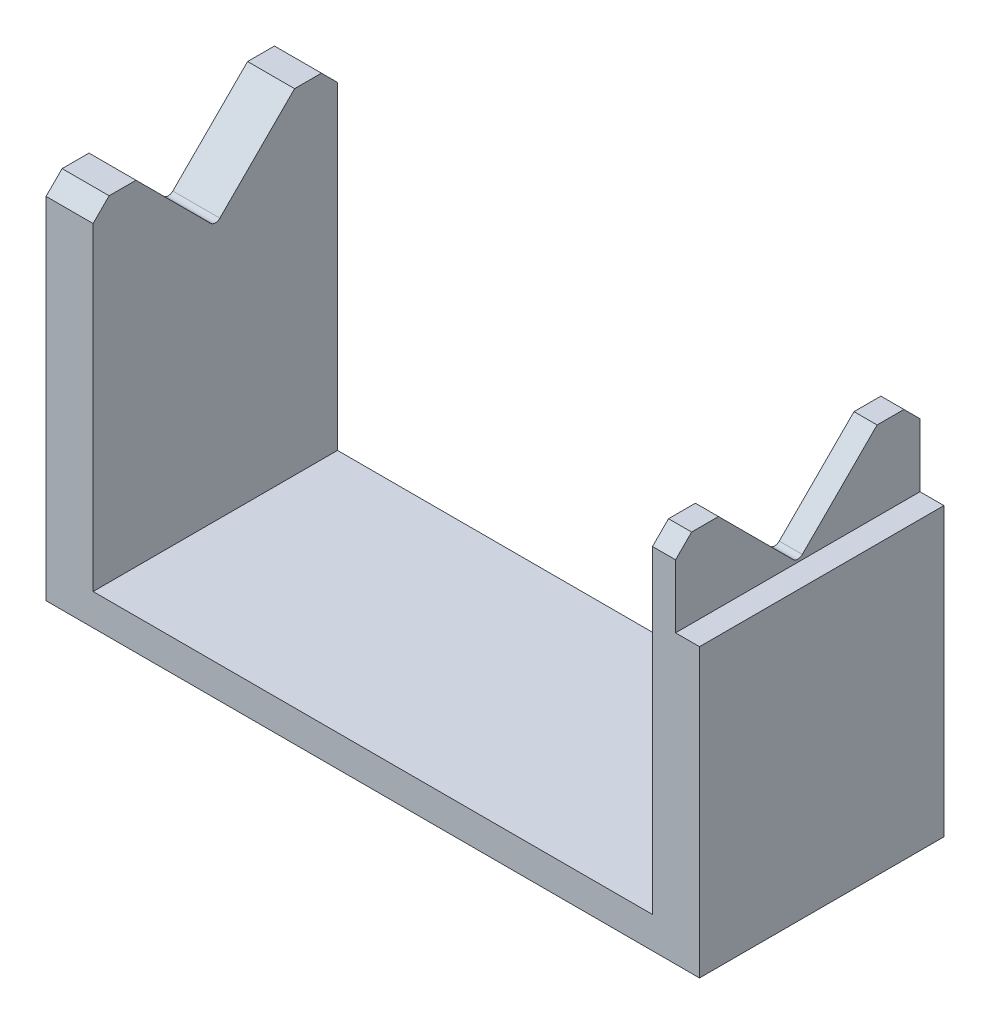
SolidWorks part; units mm, degrees
ref_plane "Plano frontal" through (0, 0, 0) normal (0, 0, 1) x (1, 0, 0)
ref_plane "Plano superior" through (0, 0, 0) normal (0, 1, 0) x (1, 0, 0)
ref_plane "Plano direito" through (0, 0, 0) normal (1, 0, 0) x (0, 0, -1)
sketch "Esboço1" plane through (0, 0, 0) normal (0, 1, 0) x (1, 0, 0)
  line L1 (50.93, -19.05) -> (-50.93, -19.05)
  line L2 (50.93, -19.05) -> (50.93, 19.05)
  line L3 (50.93, 19.05) -> (-50.93, 19.05)
  line L4 (-50.93, -19.05) -> (-50.93, 19.05)
  line L5 (50.93, -19.05) -> (-50.93, 19.05) construction
  line L6 (50.93, 19.05) -> (-50.93, -19.05) construction
  point P0 (0, 0)
  dimension "D1" = 101.86
  dimension "D2" = 38.1
extrude "Ressalto-extrusão1" add sketch "Esboço1" along normal blind 57.09
sketch "Esboço2" plane through (0, 0, 19.05) normal (0, 0, 1) x (1, 0, 0)
  line L0 (-43.6, 57.09) -> (43.6, 57.09)
  line L5 (-43.6, 57.09) -> (-43.6, 0)
  line L6 (-43.6, 57.09) -> (-43.6, 4.91)
  line L8 (43.6, 57.09) -> (43.6, 0)
  line L9 (43.6, 57.09) -> (43.6, 4.91)
  line L11 (-50.93, 4.91) -> (50.93, 4.91)
  line L12 (-43.6, 4.91) -> (43.6, 4.91)
  dimension "D1" = 7.33
  dimension "D2" = 7.33
  dimension "D3" = 4.91
extrude "Corte-extrusão1" cut sketch "Esboço2" against normal blind 57.09
sketch "Esboço4" plane through (0, 0, 19.05) normal (0, 0, 1) x (1, 0, 0)
  line L1 (50.93, 57.09) -> (50.93, 0) construction
  line L2 (50.93, 44.73) -> (47.2, 44.73) construction
  line L4 (47.2, 44.73) -> (50.93, 44.73)
  line L5 (47.2, 44.73) -> (47.2, 57.09)
  line L6 (47.2, 57.09) -> (50.93, 57.09)
  line L7 (50.93, 44.73) -> (50.93, 57.09)
extrude "Corte-extrusão2" cut sketch "Esboço4" against normal blind 57.09
sketch "Esboço5" plane through (47.2, 0, 0) normal (1, 0, 0) x (0, 0, -1)
  line L0 (0, 44.73) -> (0, 57.09) construction
  line L1 (19.05, 44.73) -> (-19.05, 44.73) construction
  line L2 (19.05, 57.09) -> (-19.05, 57.09) construction
  line L3 (0, 44.73) -> (-12.36, 57.09)
  line L4 (0, 44.73) -> (12.36, 57.09)
  line L5 (-12.36, 57.09) -> (12.36, 57.09)
extrude "Corte-extrusão3" cut sketch "Esboço5" against normal blind 1000
fillet "Filete1" radius 1 2 edges at (-47.265, 44.73, 0) (45.4, 44.73, 0)
chamfer "Chanfro1" distance 2.5 angle 45 4 edges at (-47.265, 57.09, 19.05) (-47.265, 57.09, -19.05) (45.4, 57.09, -19.05) (45.4, 57.09, 19.05)
